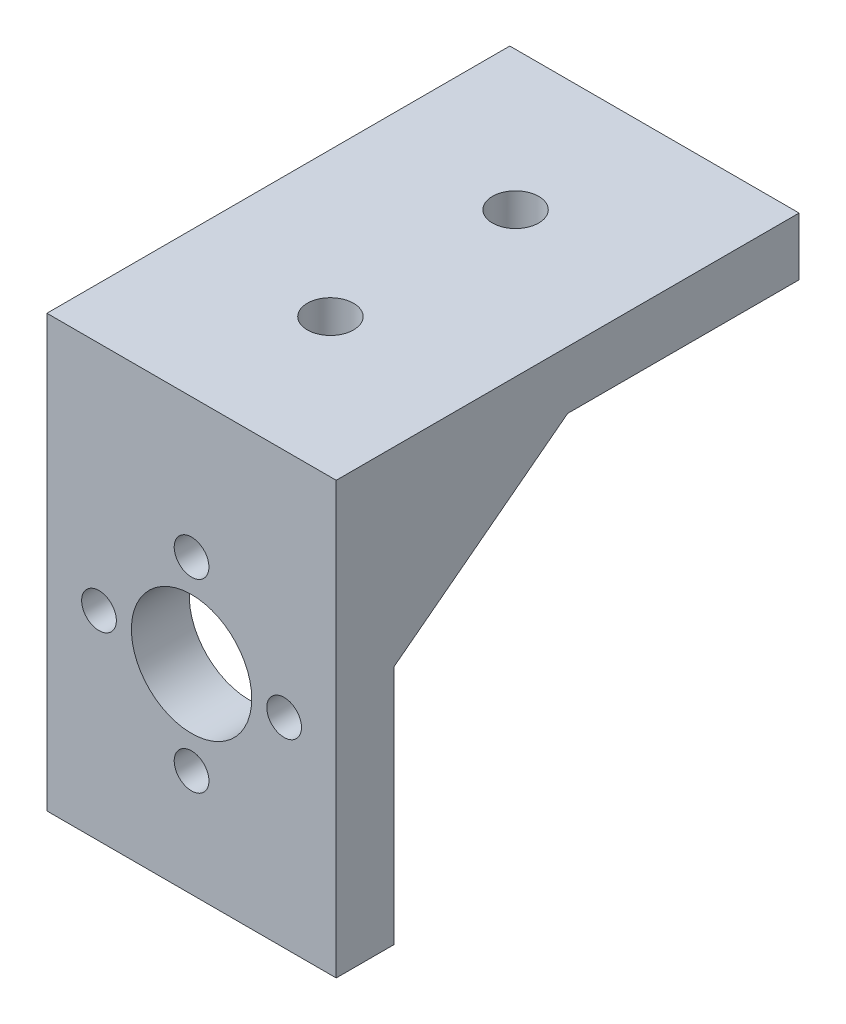
SolidWorks part; units mm, degrees
ref_plane "Front Plane" through (0, 0, 0) normal (0, 0, 1) x (1, 0, 0)
ref_plane "Top Plane" through (0, 0, 0) normal (0, 1, 0) x (1, 0, 0)
ref_plane "Right Plane" through (0, 0, 0) normal (1, 0, 0) x (0, 0, -1)
sketch "Sketch1" plane through (0, 0, 0) normal (0, 1, 0) x (1, 0, 0)
  line L1 (12.5, 20) -> (-12.5, 20)
  line L2 (12.5, 20) -> (12.5, -20)
  line L3 (12.5, -20) -> (-12.5, -20)
  line L4 (-12.5, 20) -> (-12.5, -20)
  line L5 (12.5, 20) -> (-12.5, -20) construction
  line L6 (12.5, -20) -> (-12.5, 20) construction
  point P0 (0, 0)
extrude "Boss-Extrude1" add sketch "Sketch1" along normal blind 5
sketch "Sketch2" plane through (0, 5, 0) normal (0, 1, 0) x (1, 0, 0)
  line L0 (12.5, 20) -> (-12.5, 20) construction
  circle A0 centre (0, 8) radius 2
  dimension "D1" = 12
extrude "Cut-Extrude1" cut sketch "Sketch2" against normal blind 11.5
mirror "Mirror1" about plane through (0, 0, 0) normal (0, 0, 1) of "Cut-Extrude1"
sketch "Sketch3" plane through (0, 0, 0) normal (0, -1, 0) x (1, 0, 0)
  line L0 (-12.5, -20) -> (-12.5, 20) construction
  line L1 (12.5, 20) -> (-12.5, 20)
  line L2 (12.5, 20) -> (12.5, 15)
  line L3 (12.5, 15) -> (-12.5, 15)
  line L4 (-12.5, 20) -> (-12.5, 15)
extrude "Boss-Extrude2" add sketch "Sketch3" along normal blind 32.25
sketch "Sketch5" plane through (0, 0, 20) normal (0, 0, 1) x (1, 0, 0)
  line L0 (12.5, -32.25) -> (-12.5, -32.25) construction
  circle A0 centre (0, -15) radius 11.1
  dimension "D1" = 17.25
extrude "Cut-Extrude2" cut sketch "Sketch5" against normal blind 1.5
sketch "Sketch6" plane through (0, 0, 18.5) normal (0, 0, 1) x (1, 0, 0)
  circle A0 centre (0, -15) radius 5.2
  circle A1 centre (0, -15) radius 11.1 construction
  dimension "D1" = 0
extrude "Cut-Extrude3" cut sketch "Sketch6" against normal blind 10.5
sketch "Sketch7" plane through (0, 0, 18.5) normal (0, 0, 1) x (1, 0, 0)
  circle A0 centre (0, -7) radius 1.5
  circle A1 centre (0, -15) radius 5.2 construction
  dimension "D1" = 8
extrude "Cut-Extrude4" cut sketch "Sketch7" against normal blind 10.5
pattern_circular "CirPattern1" count 4 over 360 about axis through (0, -15, 0) along (0, 0, 1) of "Cut-Extrude4"
sketch "Sketch8" plane through (-12.5, 0, 0) normal (-1, 0, 0) x (0, 0, 1)
  line L0 (15, 0) -> (0, 0)
  line L1 (0, 0) -> (15, -11.4464)
  line L3 (15, -11.4464) -> (15, 0)
  line L5 (15, -32.25) -> (15, 0) construction
extrude "Boss-Extrude3" add sketch "Sketch8" against normal blind 3
mirror "Mirror2" about plane through (0, 0, 0) normal (1, 0, 0) of "Boss-Extrude3"
sketch "Sketch9" plane through (0, 0, 18.5) normal (0, 0, 1) x (1, 0, 0)
  circle A0 centre (0, -15) radius 5.2
  circle A1 centre (0, -7) radius 1.5
  circle A2 centre (-8, -15) radius 1.5
  circle A3 centre (8, -15) radius 1.5
  circle A4 centre (0, -23) radius 1.5
  circle A5 centre (0, -15) radius 11.1
extrude "Boss-Extrude4" add sketch "Sketch9" along normal blind 1.5
